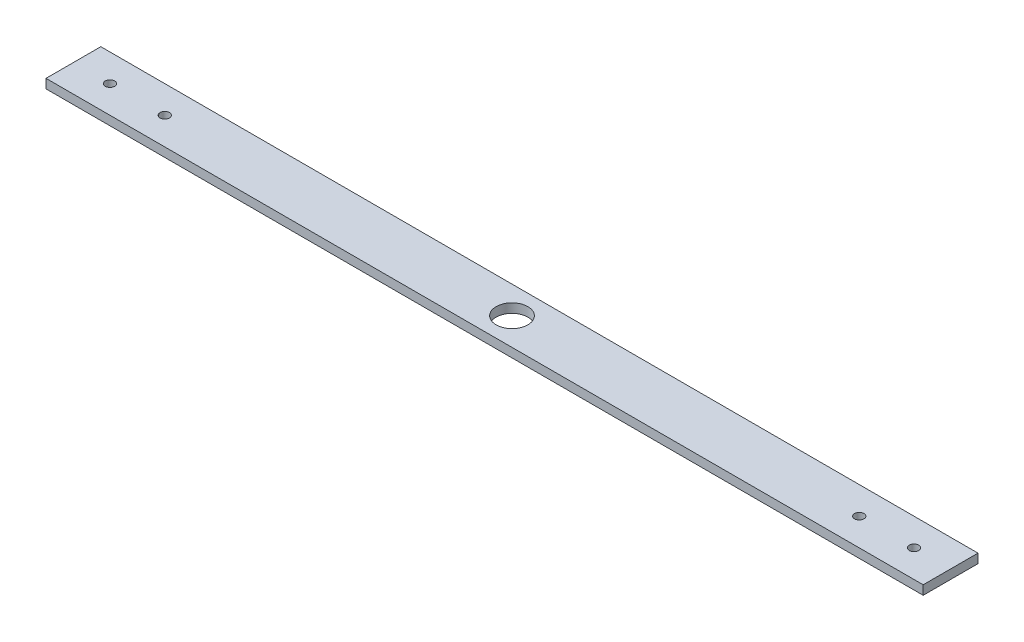
SolidWorks part; units mm, degrees
material "6061-T6 (SS)"
ref_plane "Front Plane" through (0, 0, 0) normal (0, 0, 1) x (1, 0, 0)
ref_plane "Top Plane" through (0, 0, 0) normal (0, 1, 0) x (1, 0, 0)
ref_plane "Right Plane" through (0, 0, 0) normal (1, 0, 0) x (0, 0, -1)
sketch "Sketch1" plane through (0, 0, 0) normal (0, 1, 0) x (1, 0, 0)
  line L1 (-304.8, -19.05) -> (304.8, -19.05)
  line L2 (-304.8, -19.05) -> (-304.8, 19.05)
  line L3 (-304.8, 19.05) -> (304.8, 19.05)
  line L4 (304.8, -19.05) -> (304.8, 19.05)
  line L5 (-304.8, -19.05) -> (304.8, 19.05) construction
  line L6 (-304.8, 19.05) -> (304.8, -19.05) construction
  point P0 (0, 0)
  dimension "D1" = 609.6
  dimension "D2" = 38.1
extrude "Boss-Extrude1" add sketch "Sketch1" along normal blind 6.35
sketch "Sketch2" plane through (0, 6.35, 0) normal (0, 1, 0) x (1, 0, 0)
  circle A0 centre (0, 0) radius 11
  dimension "D1" = 22
extrude "Cut-Extrude1" cut sketch "Sketch2" against normal blind 7.62
hole_wizard "F (0.257) Diameter Hole2" positions "Sketch3" profile "Sketch4" hole size "F" standard "ANSI Inch" end condition through all
sketch "Sketch3" plane through (0, 6.35, 0) normal (0, 1, 0) x (1, 0, 0)
  line L0 (0, 0) -> (-304.8, 0) construction
  line L1 (-304.8, 19.05) -> (-304.8, -19.05) construction
  point P7 (-279.4, 0)
  point P9 (-241.3, 0)
  dimension "D1" = 25.4
  dimension "D2" = 63.5
sketch "Sketch4" plane through (-241.3, 6.35, 0) normal (1, 0, 0) x (0, 0, 1)
  line L0 (0, 0) -> (0, 6.35)
  line L1 (0, 6.35) -> (3.2639, 6.35)
  line L2 (3.2639, 6.35) -> (3.2639, 0)
  line L5 (3.2639, 0) -> (0, 0)
  line L11 (0, -6.35) -> (0, 107.95) construction
  dimension "Thru Hole Dia." = 6.5278
  dimension "Thru Hole Depth" = 6.35
mirror "Mirror1" about plane through (0, 0, 0) normal (1, 0, 0) of "F (0.257) Diameter Hole2"
